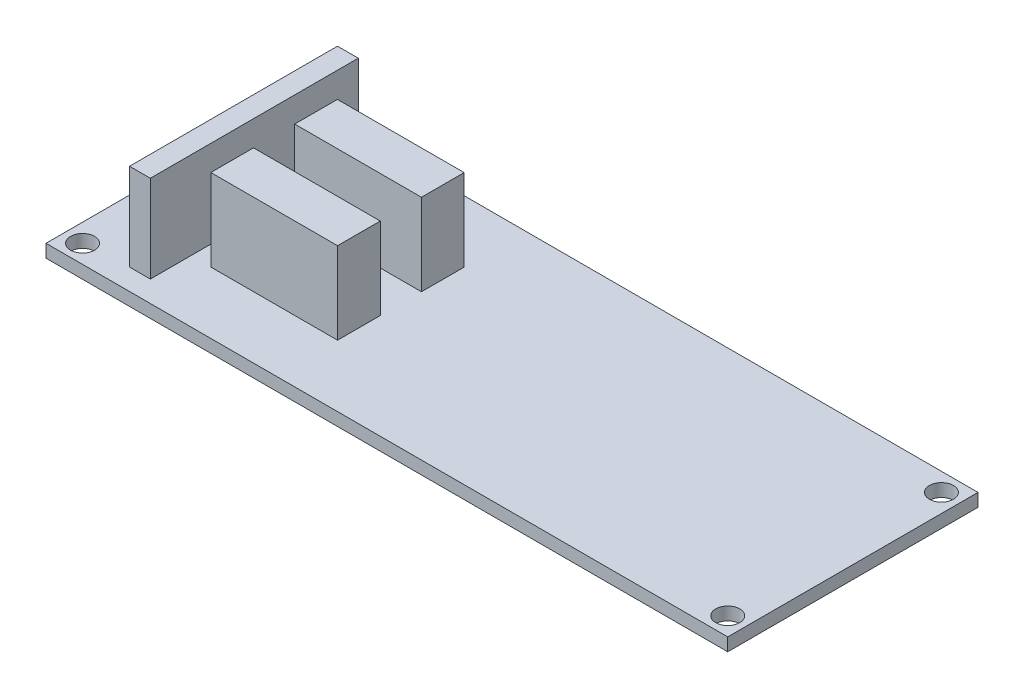
SolidWorks part; units mm, degrees
material "Glass Epoxy Composite"
ref_plane "Front Plane" through (0, 0, 0) normal (0, 0, 1) x (1, 0, 0)
ref_plane "Top Plane" through (0, 0, 0) normal (0, 1, 0) x (1, 0, 0)
ref_plane "Right Plane" through (0, 0, 0) normal (1, 0, 0) x (0, 0, -1)
sketch "Sketch1" plane through (0, 0, 0) normal (0, 1, 0) x (1, 0, 0)
  line L1 (-41.6369, -15.2844) -> (41.637, -15.2844)
  line L2 (-41.6369, -15.2844) -> (-41.6369, 15.2845)
  line L3 (-41.6369, 15.2845) -> (41.637, 15.2845)
  line L4 (41.637, -15.2844) -> (41.637, 15.2845)
  line L5 (-41.6369, -15.2844) -> (41.637, 15.2845) construction
  line L6 (-41.6369, 15.2845) -> (41.637, -15.2844) construction
  point P0 (0, 0)
  dimension "D1" = 30.5689
  dimension "D2" = 83.2739
extrude "Proton PCB " add sketch "Sketch1" along normal blind 1.5811
sketch "Sketch2" plane through (0, 1.5811, 0) normal (0, 1, 0) x (1, 0, 0)
  line L0 (-41.6369, 15.2845) -> (-41.6369, -15.2844) construction
  line L1 (-29.0575, 2.5164) -> (-13.5764, 2.5164)
  line L6 (-29.0575, 2.5164) -> (-29.0575, 7.7325)
  line L7 (-29.0575, 7.7325) -> (-13.5764, 7.7325)
  line L8 (-13.5764, 2.5164) -> (-13.5764, 7.7325)
  line L9 (-29.0575, 2.5164) -> (-13.5764, 7.7325) construction
  line L10 (-29.0575, 7.7325) -> (-13.5764, 2.5164) construction
  line L11 (41.637, 15.2845) -> (-41.6369, 15.2845) construction
  line L12 (0, 0) -> (-41.6369, 0) construction
  line L13 (-29.0575, -7.7325) -> (-13.5764, -7.7325)
  line L14 (-13.5764, -2.5164) -> (-13.5764, -7.7325)
  line L15 (-29.0575, -2.5164) -> (-13.5764, -2.5164)
  line L16 (-29.0575, -2.5164) -> (-29.0575, -7.7325)
  point P0 (-21.3169, 5.1245)
  point P3 (-22.0462, 3.81)
  dimension "D1" = 5.2161
  dimension "D2" = 15.4812
  dimension "D3" = 20.32
  dimension "D4" = 10.16
extrude "JST 6 pin Connectors" add sketch "Sketch2" along normal blind 10
sketch "Sketch3" plane through (0, 1.5811, 0) normal (0, 1, 0) x (1, 0, 0)
  line L0 (0, 0) -> (-41.6369, 0) construction
  line L1 (-31.4769, 12.7) -> (-34.0169, 12.7)
  line L2 (-31.4769, 12.7) -> (-31.4769, -12.7)
  line L3 (-31.4769, -12.7) -> (-34.0169, -12.7)
  line L4 (-34.0169, 12.7) -> (-34.0169, -12.7)
  line L5 (-31.4769, 12.7) -> (-34.0169, -12.7) construction
  line L6 (-31.4769, -12.7) -> (-34.0169, 12.7) construction
  line L7 (-41.6369, 15.2845) -> (-41.6369, -15.2844) construction
  point P0 (-32.7469, 0)
  dimension "D1" = 25.4
  dimension "D2" = 2.54
  dimension "D3" = 10.16
extrude "Boss-Extrude1" add sketch "Sketch3" along normal blind 10.668
sketch "Sketch4" plane through (0, 1.5811, 0) normal (0, 1, 0) x (1, 0, 0)
  line L14 (-39.4033, 13.0508) -> (-39.4033, -13.0508)
  line L15 (-39.4033, -13.0508) -> (39.4033, -13.0508)
  line L16 (39.4033, -13.0508) -> (39.4033, 13.0508)
  line L17 (39.4033, 13.0508) -> (-39.4033, 13.0508)
  line L18 (-39.4033, 13.0508) -> (-39.4033, -13.0508) construction
  line L19 (-39.4033, -13.0508) -> (39.4033, -13.0508) construction
  line L20 (39.4033, -13.0508) -> (39.4033, 13.0508) construction
  line L21 (39.4033, 13.0508) -> (-39.4033, 13.0508) construction
  circle A0 centre (-39.4033, 13.0508) radius 1.4653
  circle A1 centre (39.4033, 13.0508) radius 1.4653
  circle A2 centre (-39.4033, -13.0508) radius 1.4653
  circle A3 centre (39.4033, -13.0508) radius 1.4653
  dimension "D2" = 2.9305
  dimension "D1" = 2.2336
extrude "Cut-Extrude1" cut sketch "Sketch4" against normal up to surface (1.5811 mm away) up to face at (0, 0, 0)
sketch "Sketch5" plane through (0, 0, 0) normal (0, -1, 0) x (1, 0, 0)
  line L0 (0, 0) -> (-41.6369, 0) construction
  line L7 (-22.8409, 7.6644) -> (-18.2689, 7.6644)
  line L8 (-22.8409, 7.6644) -> (-22.8409, 11.2204)
  line L9 (-22.8409, 11.2204) -> (-18.2689, 11.2204)
  line L10 (-18.2689, 7.6644) -> (-18.2689, 11.2204)
  line L11 (-22.8409, 7.6644) -> (-18.2689, 11.2204) construction
  line L12 (-22.8409, 11.2204) -> (-18.2689, 7.6644) construction
  line L13 (-28.1749, 7.6644) -> (-23.6029, 7.6644)
  line L14 (-28.1749, 7.6644) -> (-28.1749, 11.2204)
  line L15 (-28.1749, 11.2204) -> (-23.6029, 11.2204)
  line L16 (-23.6029, 7.6644) -> (-23.6029, 11.2204)
  line L17 (-28.1749, 7.6644) -> (-23.6029, 11.2204) construction
  line L18 (-28.1749, 11.2204) -> (-23.6029, 7.6644) construction
  line L19 (-17.5069, 7.6644) -> (-12.9349, 7.6644)
  line L20 (-17.5069, 7.6644) -> (-17.5069, 11.2204)
  line L21 (-17.5069, 11.2204) -> (-12.9349, 11.2204)
  line L22 (-12.9349, 7.6644) -> (-12.9349, 11.2204)
  line L23 (-17.5069, 7.6644) -> (-12.9349, 11.2204) construction
  line L24 (-17.5069, 11.2204) -> (-12.9349, 7.6644) construction
  line L25 (21.317, -4.6165) -> (25.889, -4.6165)
  line L26 (21.317, -4.6165) -> (21.317, -1.0605)
  line L27 (21.317, -1.0605) -> (25.889, -1.0605)
  line L28 (25.889, -4.6165) -> (25.889, -1.0605)
  line L29 (21.317, -4.6165) -> (25.889, -1.0605) construction
  line L30 (21.317, -1.0605) -> (25.889, -4.6165) construction
  line L31 (-41.6369, -15.2845) -> (-41.6369, 15.2844) construction
  line L32 (-41.6369, 15.2844) -> (41.637, 15.2844) construction
  line L33 (-12.9349, -7.6644) -> (-12.9349, -11.2204)
  line L34 (-17.5069, -11.2204) -> (-12.9349, -11.2204)
  line L35 (-17.5069, -7.6644) -> (-17.5069, -11.2204)
  line L36 (-17.5069, -7.6644) -> (-12.9349, -7.6644)
  line L37 (-22.8409, -7.6644) -> (-18.2689, -7.6644)
  line L38 (-18.2689, -7.6644) -> (-18.2689, -11.2204)
  line L39 (-22.8409, -11.2204) -> (-18.2689, -11.2204)
  line L40 (-22.8409, -7.6644) -> (-22.8409, -11.2204)
  line L41 (-23.6029, -7.6644) -> (-23.6029, -11.2204)
  line L42 (-28.1749, -11.2204) -> (-23.6029, -11.2204)
  line L43 (-28.1749, -7.6644) -> (-28.1749, -11.2204)
  line L44 (-28.1749, -7.6644) -> (-23.6029, -7.6644)
  line L45 (41.637, 15.2844) -> (41.637, -15.2845) construction
  line L46 (41.637, -15.2845) -> (-41.6369, -15.2845) construction
  point P0 (-2.5981, 8.1672)
  point P5 (-20.5549, 9.4424)
  point P10 (-25.8889, 9.4424)
  point P15 (-15.2209, 9.4424)
  point P20 (23.603, -2.8385)
  dimension "D1" = 4.572
  dimension "D2" = 3.556
  dimension "D3" = 15.24
  dimension "D4" = 0.762
  dimension "D5" = 7.62
  dimension "D6" = 28.702
  dimension "D7" = 20.32
  dimension "D8" = 14.224
extrude "Boss-Extrude2" add sketch "Sketch5" along normal blind 1.778
sketch "Sketch6" plane through (0, 0, 0) normal (0, -1, 0) x (1, 0, 0)
  line L0 (-41.6369, -15.2845) -> (-41.6369, 15.2844) construction
  line L1 (-11.1569, 3.3464) -> (6.6231, 3.3464)
  line L2 (-11.1569, 3.3464) -> (-11.1569, 10.2044)
  line L3 (-11.1569, 10.2044) -> (6.6231, 10.2044)
  line L4 (6.6231, 3.3464) -> (6.6231, 10.2044)
  line L5 (-11.1569, 3.3464) -> (6.6231, 10.2044) construction
  line L6 (-11.1569, 10.2044) -> (6.6231, 3.3464) construction
  line L7 (-41.6369, 15.2844) -> (41.637, 15.2844) construction
  point P0 (-2.2669, 6.7755)
  dimension "D1" = 17.78
  dimension "D2" = 6.858
  dimension "D3" = 48.26
  dimension "D4" = 11.938
extrude "Boss-Extrude3" add sketch "Sketch6" along normal blind 2.794
